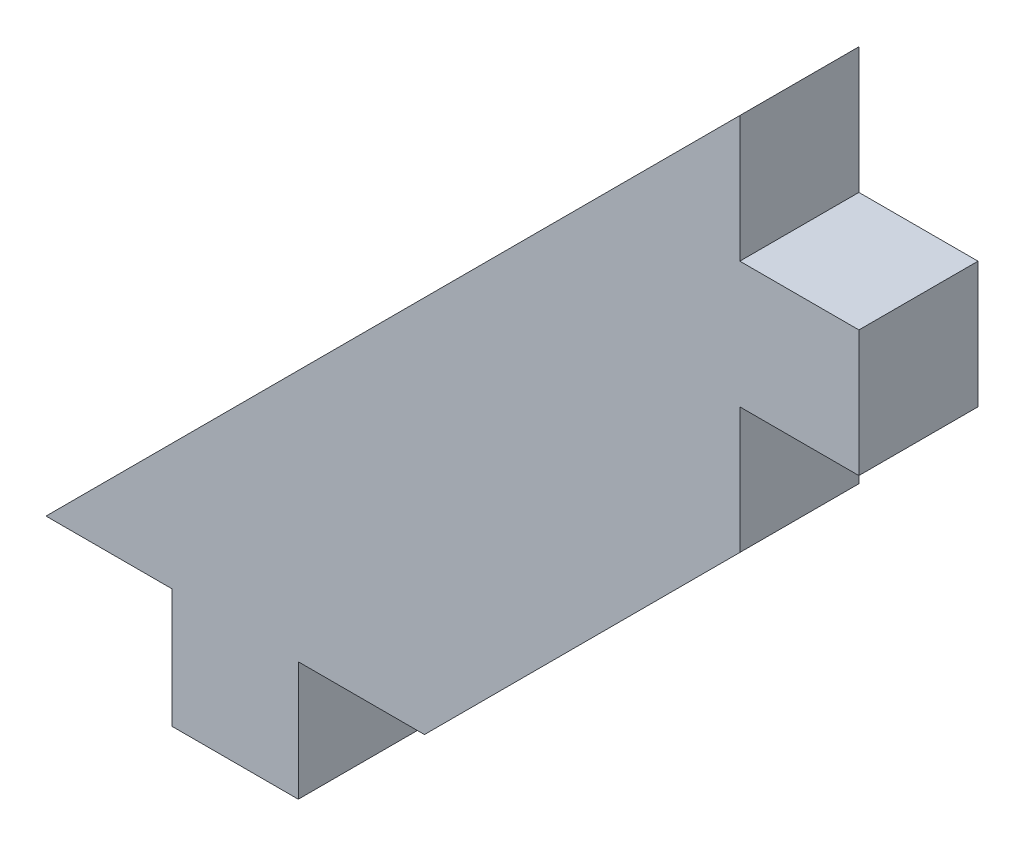
SolidWorks part; units mm, degrees
material "Acrylic (Medium-high impact)"
ref_plane "Front Plane" through (0, 0, 0) normal (0, 0, 1) x (1, 0, 0)
ref_plane "Top Plane" through (0, 0, 0) normal (0, 1, 0) x (1, 0, 0)
ref_plane "Right Plane" through (0, 0, 0) normal (1, 0, 0) x (0, 0, -1)
sketch "Sketch1" plane through (0, 0, 0) normal (0, 0, 1) x (1, 0, 0)
  line L0 (-6.35, 5.9944) -> (0, 5.9944)
  line L1 (0, 5.9944) -> (0, 0)
  line L2 (0, 0) -> (6.35, 0)
  line L3 (6.35, 0) -> (6.35, 5.9944)
  line L4 (6.35, 5.9944) -> (12.7, 5.9944)
  line L5 (12.7, 5.9944) -> (28.575, 21.8694)
  line L6 (28.575, 21.8694) -> (28.575, 28.2194)
  line L7 (28.575, 28.2194) -> (34.5694, 28.2194)
  line L8 (34.5694, 34.5694) -> (34.5694, 28.2194)
  line L17 (34.5694, 34.5694) -> (28.575, 34.5694)
  line L18 (28.575, 34.5694) -> (28.575, 40.9194)
  line L19 (28.575, 40.9194) -> (-6.35, 5.9944)
  dimension "D1" = 45
  dimension "D2" = 5.9944
  dimension "D3" = 6.35
  dimension "D4" = 5.9944
  dimension "D5" = 28.575
extrude "Boss-Extrude1" add sketch "Sketch1" along normal blind 5.9944
